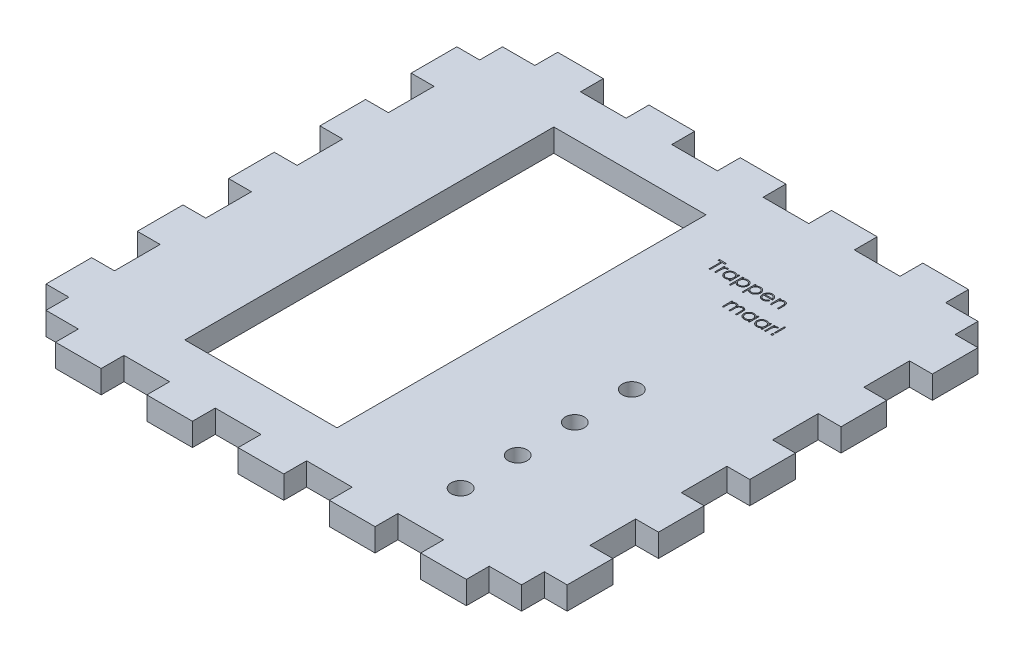
SolidWorks part; units mm, degrees
ref_plane "Front Plane" through (0, 0, 0) normal (0, 0, 1) x (1, 0, 0)
ref_plane "Top Plane" through (0, 0, 0) normal (0, 1, 0) x (1, 0, 0)
ref_plane "Right Plane" through (0, 0, 0) normal (1, 0, 0) x (0, 0, -1)
sketch "Sketch1" plane through (0, 0, 0) normal (0, 1, 0) x (1, 0, 0)
  line L0 (2.5, 48.5) -> (2.5, 60) construction
  line L1 (-62.5, -60) -> (62.5, -60)
  line L2 (-62.5, -60) -> (-62.5, 60)
  line L3 (-62.5, 60) -> (62.5, 60)
  line L4 (62.5, -60) -> (62.5, 60)
  line L5 (-62.5, -60) -> (62.5, 60) construction
  line L6 (-62.5, 60) -> (62.5, -60) construction
  line L7 (-37.5, -48.5) -> (2.5, -48.5)
  line L8 (-37.5, -48.5) -> (-37.5, 48.5)
  line L9 (-37.5, 48.5) -> (2.5, 48.5)
  line L10 (2.5, -48.5) -> (2.5, 48.5)
  line L11 (-37.5, -48.5) -> (2.5, 48.5) construction
  line L12 (-37.5, 48.5) -> (2.5, -48.5) construction
  line L13 (2.5, -48.5) -> (2.5, -60) construction
  line L14 (-37.5, 48.5) -> (-62.5, 48.5) construction
  line L15 (32.5, -46) -> (32.5, -31) construction
  line L16 (2.5, -48.5) -> (32.5, -48.5) construction
  line L17 (32.5, -31) -> (32.5, -16) construction
  line L18 (32.5, -16) -> (32.5, -1) construction
  line L19 (32.5, -48.5) -> (62.5, -48.5) construction
  line L20 (-54, 66) -> (-54, 60)
  line L21 (-62.5, 54) -> (-68.5, 54)
  line L22 (-54, 66) -> (-42, 66)
  line L23 (-42, 66) -> (-42, 60)
  line L24 (-18, 66) -> (-18, 60)
  line L25 (-30, 66) -> (-30, 60)
  line L26 (-30, 66) -> (-18, 66)
  line L27 (6, 66) -> (6, 60)
  line L28 (-6, 66) -> (-6, 60)
  line L29 (-6, 66) -> (6, 66)
  line L30 (30, 66) -> (30, 60)
  line L31 (18, 66) -> (18, 60)
  line L32 (18, 66) -> (30, 66)
  line L33 (54, 66) -> (54, 60)
  line L34 (42, 66) -> (42, 60)
  line L35 (42, 66) -> (54, 66)
  line L36 (-68.5, 54) -> (-68.5, 42)
  line L37 (-68.5, 42) -> (-62.5, 42)
  line L38 (-62.5, 30) -> (-68.5, 30)
  line L39 (-68.5, 30) -> (-68.5, 18)
  line L40 (-68.5, 18) -> (-62.5, 18)
  line L41 (-62.5, 6) -> (-68.5, 6)
  line L42 (-68.5, 6) -> (-68.5, -6)
  line L43 (-68.5, -6) -> (-62.5, -6)
  line L44 (-62.5, -18) -> (-68.5, -18)
  line L45 (-68.5, -18) -> (-68.5, -30)
  line L46 (-68.5, -30) -> (-62.5, -30)
  line L47 (-62.5, -42) -> (-68.5, -42)
  line L48 (-68.5, -42) -> (-68.5, -54)
  line L49 (-68.5, -54) -> (-62.5, -54)
  line L51 (0, -55) -> (0, 55) construction
  line L52 (68.5, -54) -> (62.5, -54)
  line L53 (68.5, -42) -> (68.5, -54)
  line L54 (62.5, -42) -> (68.5, -42)
  line L55 (68.5, -30) -> (62.5, -30)
  line L56 (68.5, -18) -> (68.5, -30)
  line L57 (62.5, -18) -> (68.5, -18)
  line L58 (68.5, -6) -> (62.5, -6)
  line L59 (68.5, 6) -> (68.5, -6)
  line L60 (62.5, 6) -> (68.5, 6)
  line L61 (68.5, 18) -> (62.5, 18)
  line L62 (68.5, 30) -> (68.5, 18)
  line L63 (62.5, 30) -> (68.5, 30)
  line L64 (68.5, 42) -> (62.5, 42)
  line L65 (68.5, 54) -> (68.5, 42)
  line L66 (-55, 0) -> (55, 0) construction
  line L67 (42, -66) -> (54, -66)
  line L68 (42, -66) -> (42, -60)
  line L69 (54, -66) -> (54, -60)
  line L70 (18, -66) -> (30, -66)
  line L71 (18, -66) -> (18, -60)
  line L72 (30, -66) -> (30, -60)
  line L73 (-6, -66) -> (6, -66)
  line L74 (-6, -66) -> (-6, -60)
  line L75 (6, -66) -> (6, -60)
  line L76 (-30, -66) -> (-18, -66)
  line L77 (-30, -66) -> (-30, -60)
  line L78 (-18, -66) -> (-18, -60)
  line L79 (-42, -66) -> (-42, -60)
  line L80 (-54, -66) -> (-42, -66)
  line L81 (-54, -66) -> (-54, -60)
  line L82 (62.5, 54) -> (68.5, 54)
  circle A0 centre (32.5, -1) radius 2.5
  circle A1 centre (32.5, -16) radius 2.5
  circle A2 centre (32.5, -31) radius 2.5
  circle A3 centre (32.5, -46) radius 2.5
  point P0 (0, 0)
  point P6 (-17.5, 0)
  point P108 (0, 0)
  dimension "D6" = 97
  dimension "D7" = 6
  dimension "D8" = 12
  dimension "D1" = 125
  dimension "D2" = 5
  dimension "D3" = 120
  dimension "D4" = 40
  dimension "D5" = 25
  dimension "D10" = 8.5
  dimension "D12" = 12
  dimension "D13" = 6
  dimension "D14" = 6
  dimension "D11" = 5
extrude "Boss-Extrude2" add sketch "Sketch1" along normal blind 6 contours L1 L4 L3 L2 A3 A2 A1 | L39 L40 L2 L38 | L36 L37 L2 L21 | L45 L46 L2 L44 | L42 L43 L2 L41 | L48 L49 L2 L47 | L81 L80 L79 L1 | L76 L78 L1 L77 | L73 L75 L1 L74 | L70 L72 L1 L71 | L67 L69 L1 L68 | L54 L4 L52 L53 | L57 L4 L55 L56 | L60 L4 L58 L59 | L63 L4 L61 L62 | L82 L4 L64 L65 | L35 L34 L3 L33 | L32 L31 L3 L30 | L29 L28 L3 L27 | L23 L22 L20 L3 | L26 L25 L3 L24
sketch "Sketch2" plane through (0, 6, 0) normal (0, 1, 0) x (1, 0, 0)
  text T0 "Trappen \r\n        maar!" font "Century Gothic" height 3.5
extrude "Cut-Extrude1" cut sketch "Sketch2" against normal through all
